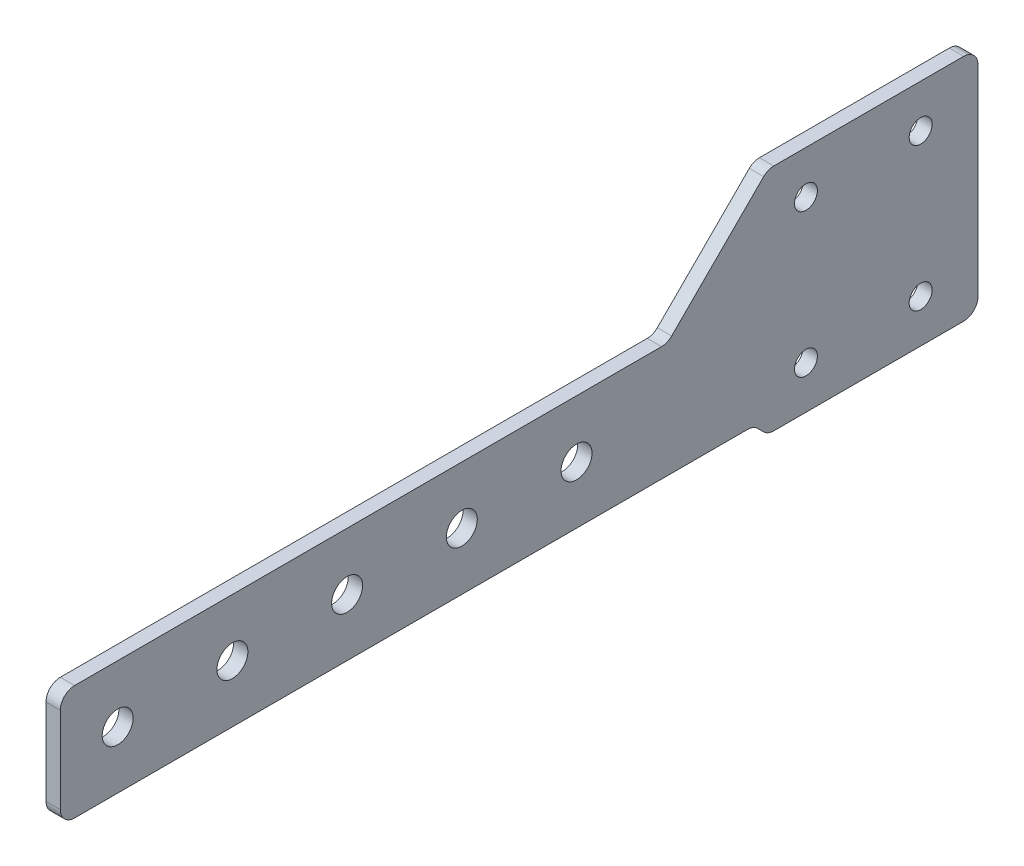
SolidWorks part; units mm, degrees
ref_plane "Front Plane" through (0, 0, 0) normal (0, 0, 1) x (1, 0, 0)
ref_plane "Top Plane" through (0, 0, 0) normal (0, 1, 0) x (1, 0, 0)
ref_plane "Right Plane" through (0, 0, 0) normal (1, 0, 0) x (0, 0, -1)
sketch "Sketch2" plane through (0, 0, 0) normal (1, 0, 0) x (0, 0, -1)
  line L0 (-111.125, 12.7) -> (18.8244, 12.7)
  line L1 (21.0694, 13.6299) -> (41.4346, 33.9951)
  line L2 (43.6796, 34.925) -> (85.725, 34.925)
  line L3 (88.9, 31.75) -> (88.9, -12.7)
  line L4 (85.725, -15.875) -> (43.6796, -15.875)
  line L5 (41.4346, -14.9451) -> (40.1194, -13.6299)
  line L6 (37.8744, -12.7) -> (-111.125, -12.7)
  line L7 (-114.3, -9.525) -> (-114.3, 9.525)
  circle A0 centre (-101.6, 0) radius 3.429
  circle A1 centre (-76.2, 0) radius 3.429
  circle A2 centre (-50.8, 0) radius 3.429
  circle A3 centre (-25.4, 0) radius 3.429
  circle A4 centre (0, 0) radius 3.429
  circle A5 centre (50.8, 25.4) radius 2.54
  circle A6 centre (76.2, 25.4) radius 2.54
  circle A7 centre (50.8, -6.35) radius 2.54
  circle A8 centre (76.2, -6.35) radius 2.54
  arc A9 (88.9, -12.7) -> (85.725, -15.875) centre (85.725, -12.7) cw
  arc A10 (85.725, 34.925) -> (88.9, 31.75) centre (85.725, 31.75) cw
  arc A11 (41.4346, 33.9951) -> (43.6796, 34.925) centre (43.6796, 31.75) cw
  arc A12 (18.8244, 12.7) -> (21.0694, 13.6299) centre (18.8244, 15.875) ccw
  arc A13 (40.1194, -13.6299) -> (37.8744, -12.7) centre (37.8744, -15.875) ccw
  arc A14 (43.6796, -15.875) -> (41.4346, -14.9451) centre (43.6796, -12.7) cw
  arc A15 (-111.125, -12.7) -> (-114.3, -9.525) centre (-111.125, -9.525) cw
  arc A16 (-111.125, 12.7) -> (-114.3, 9.525) centre (-111.125, 9.525) ccw
  point P22 (20.9687, 36.7134)
  point P28 (64.7023, 34.925)
  dimension "D2" = 12.7
  dimension "D3" = 6.858
  dimension "D4" = 12.7
  dimension "D7" = 25.4
  dimension "D11" = 5.08
  dimension "D13" = 25.4
  dimension "D14" = 25.4
  dimension "D15" = 50.8
  dimension "D16" = 31.75
  dimension "D6" = 135
  dimension "D18" = 9.525
  dimension "D10" = 12.7
  dimension "D19" = 12.7
  dimension "D20" = 3.175
  dimension "D1" = 25.4
  dimension "D8" = 9.525
  dimension "D9" = 2
  dimension "D17" = 12.7
  dimension "D5" = 5
  dimension "D12" = 2
extrude "Boss-Extrude1" add sketch "Sketch2" along normal blind 3.175
